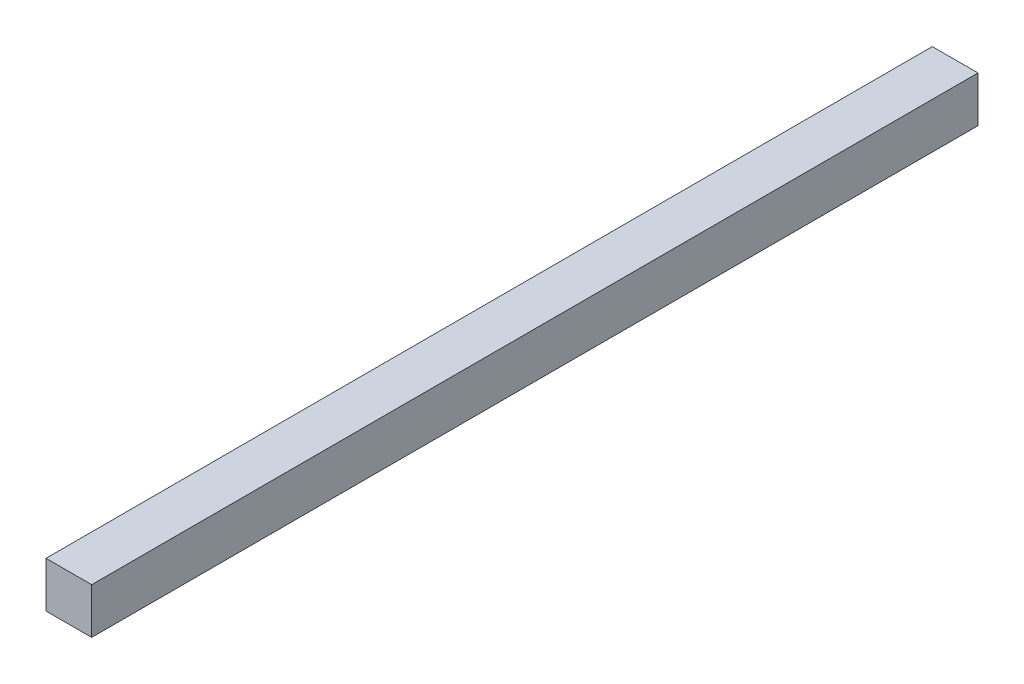
SolidWorks part; units mm, degrees
ref_plane "Front Plane" through (0, 0, 0) normal (0, 0, 1) x (1, 0, 0)
ref_plane "Top Plane" through (0, 0, 0) normal (0, 1, 0) x (1, 0, 0)
ref_plane "Right Plane" through (0, 0, 0) normal (1, 0, 0) x (0, 0, -1)
sketch "Sketch1" plane through (0, 0, 0) normal (0, 0, 1) x (1, 0, 0)
  line L1 (5, 5) -> (-5, 5)
  line L2 (5, 5) -> (5, -5)
  line L3 (5, -5) -> (-5, -5)
  line L4 (-5, 5) -> (-5, -5)
  line L5 (5, 5) -> (-5, -5) construction
  line L6 (5, -5) -> (-5, 5) construction
  point P0 (0, 0)
  dimension "D1" = 10
extrude "Boss-Extrude1" add sketch "Sketch1" along normal blind 194
sketch "Sketch3" plane through (0, 0, 0) normal (0, 0, -1) x (-1, 0, 0)
  point P0 (0, 0)
sketch "Sketch4" plane through (0, 0, 0) normal (0, 0, -1) x (-1, 0, 0)
  line L0 (5, 0) -> (-5, 0)
  line L1 (-5, -5) -> (-5, 5) construction
  point P5 (0, 0)
sketch "Sketch5" plane through (-5, 0, 0) normal (-1, 0, 0) x (0, 0, 1)
  line L0 (0, 0) -> (0, 5)
  line L1 (-0.3736, 4.1857) -> (-1.9451, 4.1857)
  line L2 (-1.9451, 4.1857) -> (-1.3515, 3.771)
  line L3 (-1.3515, 4.6003) -> (-1.3515, 3.771) construction
  line L4 (-1.3515, 4.6003) -> (-1.9451, 4.1857)
  line L5 (-2.2591, 4.1857) -> (-2.8046, 4.1857)
  line L6 (-2.5318, 4.4584) -> (-2.5318, 3.9129)
  point P10 (-1.3515, 4.1857)
  point P13 (-2.5318, 4.1857)
  dimension "D1" = 5
sketch "Sketch7" plane through (0, 0, 194) normal (0, 0, 1) x (1, 0, 0)
  line L3 (0, 0) -> (-5, 0) construction
  line L4 (-5, 5) -> (-5, -5) construction
  line L5 (-5, 0) -> (-18.82, 0) construction
  dimension "D2" = 18.82
